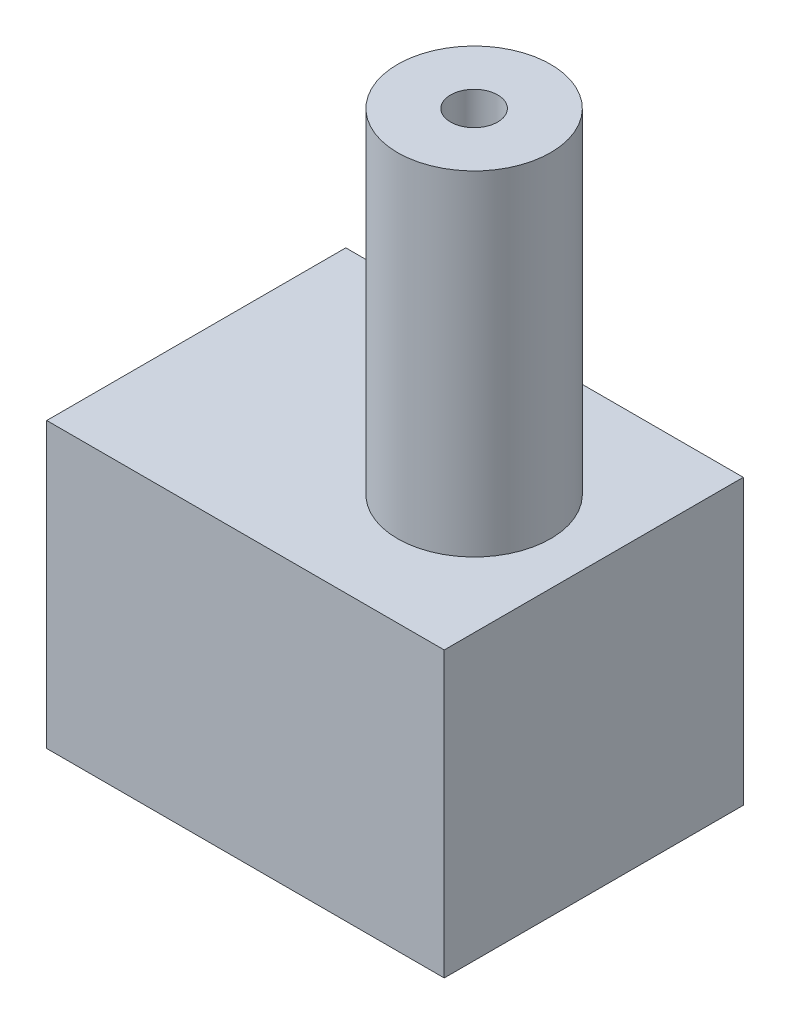
SolidWorks part; units mm, degrees
material "Brass"
ref_plane "Front Plane" through (0, 0, 0) normal (0, 0, 1) x (1, 0, 0)
ref_plane "Top Plane" through (0, 0, 0) normal (0, 1, 0) x (1, 0, 0)
ref_plane "Right Plane" through (0, 0, 0) normal (1, 0, 0) x (0, 0, -1)
sketch "Sketch1" plane through (0, 0, 0) normal (0, 1, 0) x (1, 0, 0)
  line L0 (0, 0) -> (0, 12.7)
  line L1 (0, 0) -> (16.88, 0)
  line L2 (0, 12.7) -> (16.88, 12.7)
  line L3 (16.88, 0) -> (16.88, 12.7)
  dimension "D1" = 12.7
  dimension "D2" = 16.88
extrude "Boss-Extrude1" add sketch "Sketch1" along normal blind 12.065
sketch "Sketch3" plane through (0, 12.065, 0) normal (0, 1, 0) x (1, 0, 0)
  line L0 (16.88, 0) -> (16.88, 12.7) construction
  line L1 (16.88, 12.7) -> (0, 12.7) construction
  circle A0 centre (11.8, 6.35) radius 3.25
  dimension "D1" = 6.5
  dimension "D2" = 5.08
  dimension "D3" = 6.35
extrude "Boss-Extrude2" add sketch "Sketch3" along normal blind 14.2
sketch "Sketch4" plane through (0, 26.265, 0) normal (0, 1, 0) x (1, 0, 0)
  circle A0 centre (11.8, 6.35) radius 1
  dimension "D1" = 2
extrude "Cut-Extrude1" cut sketch "Sketch4" against normal through all
